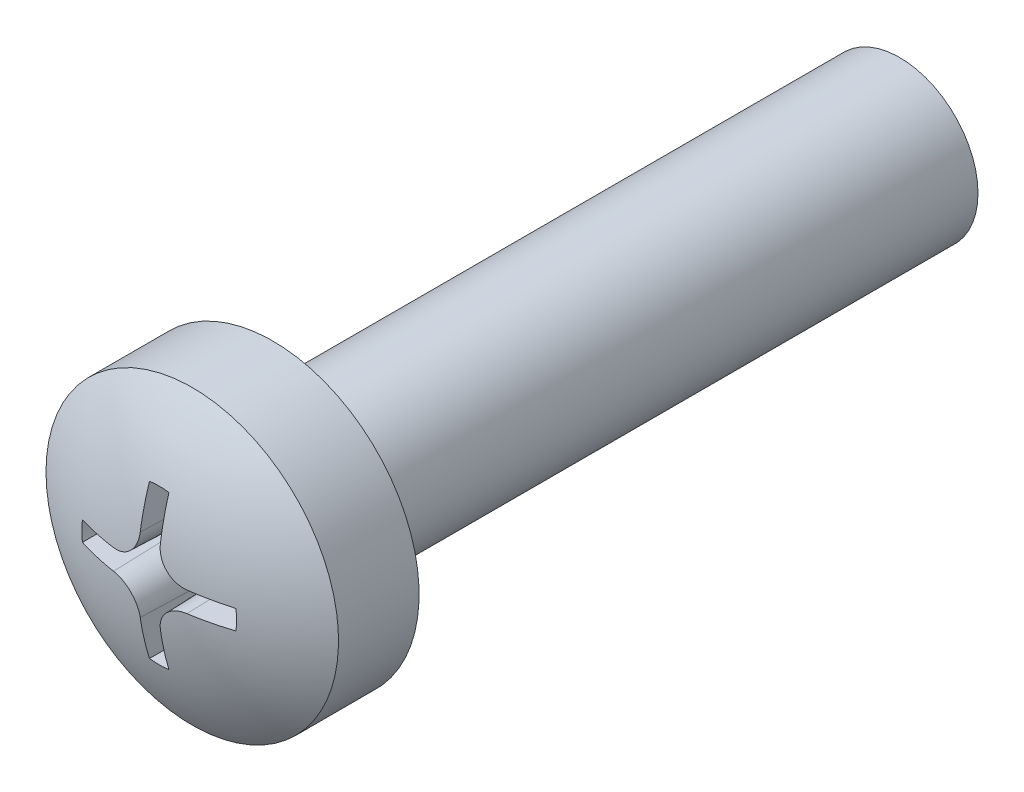
SolidWorks part; units mm, degrees
material "普通碳钢"
ref_plane "Plane1" through (0, 0, 0) normal (0, 0, 1) x (1, 0, 0)
ref_plane "Plane2" through (0, 0, 0) normal (0, 1, 0) x (1, 0, 0)
ref_plane "Plane3" through (0, 0, 0) normal (1, 0, 0) x (0, 0, -1)
sketch "Sketch1" plane through (0, 0, 0) normal (0, 0, 1) x (1, 0, 0)
  circle A0 centre (0, 0) radius 1.5
  dimension "D1" = 3
extrude "Base-Extrude" add sketch "Sketch1" along normal blind 12 and the other way blind 0.0001
sketch "Sketch6" plane through (0, 0, 0) normal (0, 1, 0) x (1, 0, 0)
  line L0 (0, 0.3936) -> (0, -34.4908) construction
  line L1 (0, -12) -> (0, 0.0001) construction
  line L2 (0, -12) -> (2.8, -12)
  line L3 (2.8, -12) -> (2.8, -13.5425)
  line L4 (0, -14.4) -> (0, -12)
  line L5 (-1.5, -12) -> (1.5, -12) construction
  arc A0 (2.8, -13.5425) -> (0, -14.4) centre (0, -9.4) cw
  dimension "D1" = 2.4
  dimension "D9" = 5
  dimension "D8" = 2.8
revolve "Boss-Revolve2" add sketch "Sketch6" angle 360 about L0
ref_plane "Plane6" through (0, 0, 14.7) normal (0, 0, -1) x (-1, 0, 0)
sketch "Sketch7" plane through (0, 0, 14.7) normal (0, 0, -1) x (-1, 0, 0)
  line L0 (-7.1, 0) -> (5.9, 0) construction
  line L1 (0, 7.5) -> (0, -7) construction
  line L2 (0.205, 1.4859) -> (0.205, 0.7082)
  line L3 (0, 0) -> (4.9858, 4.9858) construction
  line L4 (1.4859, 0.205) -> (0.703, 0.2082)
  line L5 (1.4859, -0.205) -> (0.703, -0.2082)
  line L6 (0.205, -1.4859) -> (0.205, -0.7082)
  line L7 (-0.205, -1.4859) -> (-0.205, -0.7082)
  line L8 (-1.4859, -0.205) -> (-0.703, -0.2082)
  line L9 (-1.4859, 0.205) -> (-0.703, 0.2082)
  line L10 (-0.205, 1.4859) -> (-0.205, 0.7082)
  arc A0 (-0.205, 1.4859) -> (0.205, 1.4859) centre (0, 0) cw
  arc A1 (1.4859, -0.205) -> (1.4859, 0.205) centre (0, 0) ccw
  arc A2 (0.205, 0.7082) -> (0.703, 0.2082) centre (0.705, 0.7082) ccw
  arc A3 (-0.205, 0.7082) -> (-0.703, 0.2082) centre (-0.705, 0.7082) cw
  arc A4 (-0.205, -1.4859) -> (0.205, -1.4859) centre (0, 0) ccw
  arc A5 (-0.205, -0.7082) -> (-0.703, -0.2082) centre (-0.705, -0.7082) ccw
  arc A6 (-1.4859, -0.205) -> (-1.4859, 0.205) centre (0, 0) cw
  arc A7 (0.703, -0.2082) -> (0.205, -0.7082) centre (0.705, -0.7082) ccw
  dimension "D1" = 0.5
  dimension "D10" = 1.5
  dimension "D11" = 0.41
extrude "Cut-Extrude1" cut sketch "Sketch7" along normal blind 1.8 draft 2
